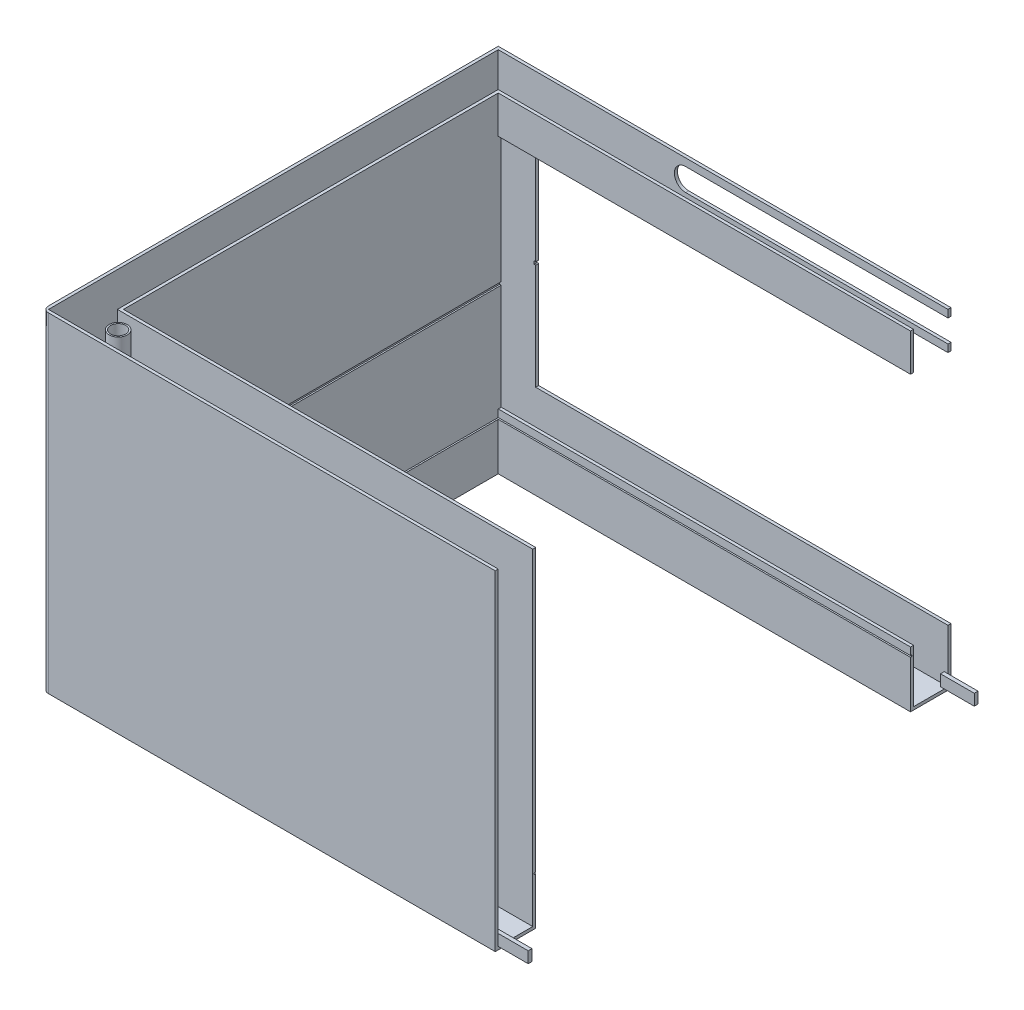
SolidWorks part; units mm, degrees
material "PVC Rigid"
ref_plane "Front Plane" through (0, 0, 0) normal (0, 0, 1) x (1, 0, 0)
ref_plane "Top Plane" through (0, 0, 0) normal (0, 1, 0) x (1, 0, 0)
ref_plane "Right Plane" through (0, 0, 0) normal (1, 0, 0) x (0, 0, -1)
sketch "Sketch1" plane through (0, 0, 0) normal (0, 1, 0) x (1, 0, 0)
  line L0 (0, -300) -> (0, 300) construction
  line L1 (0, 300) -> (-600, 300)
  line L2 (-600, 300) -> (-600, -300)
  line L3 (-600, -300) -> (0, -300)
  line L4 (0, -300) -> (0, -304)
  line L5 (0, -304) -> (-604, -304)
  line L6 (-604, -304) -> (-604, 304)
  line L7 (-604, 304) -> (0, 304)
  line L8 (0, 304) -> (0, 300)
  point P4 (0, 0)
extrude "Boss-Extrude1" add sketch "Sketch1" along normal blind 440
sketch "Sketch2" plane through (0, 0, 0) normal (0, 1, 0) x (1, 0, 0)
  line L0 (0, 0) -> (0, 250) construction
  line L1 (0, 250) -> (-550, 250)
  line L2 (-550, 250) -> (-550, -250)
  line L3 (-550, -250) -> (0, -250)
  line L4 (0, -250) -> (0, -254)
  line L5 (0, -254) -> (-554, -254)
  line L6 (-554, -254) -> (-554, 254)
  line L7 (-554, 254) -> (0, 254)
  line L8 (0, 254) -> (0, 250)
extrude "Boss-Extrude2" add sketch "Sketch2" along normal blind 440 separate body
sketch "Sketch3" plane through (0, 0, 0) normal (0, 1, 0) x (1, 0, 0)
  line L0 (0, -254) -> (0, -300)
  line L1 (0, -300) -> (-600, -300)
  line L2 (-600, -300) -> (-600, 300)
  line L3 (-600, 300) -> (0, 300)
  line L4 (0, 300) -> (0, 254)
  line L5 (0, 254) -> (-554, 254)
  line L6 (-554, 254) -> (-554, -254)
  line L7 (-554, -254) -> (0, -254)
extrude "Boss-Extrude3" add sketch "Sketch3" along normal blind 4
sketch "Sketch4" plane through (-550, 0, 0) normal (1, 0, 0) x (0, 0, -1)
  line L0 (0, 440) -> (0, 220) construction
  line L1 (-250, 440) -> (250, 440) construction
  line L2 (-250, 220) -> (250, 220)
  line L3 (250, 440) -> (250, 0) construction
  line L4 (-250, 220) -> (-250, 216)
  line L5 (-250, 440) -> (-250, 0) construction
  line L6 (-250, 216) -> (250, 216)
  line L7 (250, 216) -> (250, 220)
  line L8 (-250, 440) -> (-250, 0) construction
  point P10 (0, 220)
extrude "Cut-Extrude1" cut sketch "Sketch4" against normal blind 2
ref_plane "Plane1" through (0, 64, 0) normal (0, 1, 0) x (1, 0, 0)
sketch "Sketch7" plane through (0, 64, 0) normal (0, 1, 0) x (1, 0, 0)
  line L0 (-550, 250) -> (0, 250)
  line L1 (0, 250) -> (0, 252)
  line L2 (0, 250) -> (0, 254) construction
  line L3 (0, 252) -> (-552, 252)
  line L4 (-552, 252) -> (-552, -252)
  line L5 (-552, -252) -> (0, -252)
  line L6 (0, -254) -> (0, -250) construction
  line L7 (0, -252) -> (0, -250)
  line L8 (0, -250) -> (-550, -250)
  line L9 (-550, -250) -> (-550, 250)
extrude "Cut-Extrude3" cut sketch "Sketch7" against normal blind 1 and the other way blind 1
ref_plane "Plane2" through (0, 42, 0) normal (0, 1, 0) x (1, 0, 0)
ref_plane "Plane3" through (0, 0, 0) normal (1, 0, 0) x (0, 0, -1)
sketch "Sketch11" plane through (0, 0, 0) normal (1, 0, 0) x (0, 0, -1)
  line L0 (-295, 4) -> (-300, 4)
  line L1 (-300, 4) -> (-300, 19)
  line L9 (-300, 4) -> (-254, 4) construction
  line L10 (-300, 440) -> (-300, 4) construction
  line L11 (-295, 4) -> (-295, 19)
  line L12 (-295, 19) -> (-300, 19)
  point P0 (-295, 4)
  dimension "D1" = 5
sketch "Sketch12" plane through (0, 0, 0) normal (1, 0, 0) x (0, 0, -1)
  line L0 (254, 4) -> (300, 4) construction
  line L1 (300, 440) -> (300, 4) construction
  line L7 (300, 19) -> (295, 19)
  line L8 (295, 19) -> (295, 4)
  line L9 (295, 4) -> (300, 4)
  line L10 (300, 4) -> (300, 19)
  point P0 (295, 4)
  dimension "D1" = 5
extrude "Boss-Extrude4" add sketch "Sketch12" along normal blind 40 and the other way blind 5 separate body contours L7 L8 L9 L10
extrude "Boss-Extrude5" add sketch "Sketch11" along normal blind 40 and the other way blind 5 separate body contours L12 L1 L0 L11
sketch "Sketch13" plane through (0, 0, -304) normal (0, 0, -1) x (-1, 0, 0)
  line L0 (0, 440) -> (0, 0) construction
  line L1 (0, 440) -> (604, 440) construction
  line L2 (0, 390) -> (550, 390)
  line L3 (550, 390) -> (550, 220)
  line L4 (550, 220) -> (552, 220)
  line L5 (552, 220) -> (552, 216)
  line L8 (550, 75) -> (0, 75)
  line L9 (0, 75) -> (0, 390)
  line L10 (552, 216) -> (550, 216)
  line L11 (550, 216) -> (550, 75)
  point P0 (0, 390)
  dimension "D1" = 50
extrude "Cut-Extrude5" cut sketch "Sketch13" against normal up to vertex contours L2 L3 L4 L5 L10 L11 L8 L9
sketch "Sketch14" plane through (0, 0, -304) normal (0, 0, -1) x (-1, 0, 0)
  line L0 (0, 400) -> (0, 430)
  line L1 (0, 440) -> (0, 390) construction
  line L3 (0, 430) -> (350, 430)
  line L5 (0, 400) -> (350, 400)
  arc A0 (350, 430) -> (350, 400) centre (350, 415) cw
  point P6 (0, 415)
extrude "Cut-Extrude6" cut sketch "Sketch14" against normal blind 4
fillet "Fillet1" radius 8 1 edges at (-604, 220, 304)
sketch "Sketch15" plane through (0, 0, 0) normal (0, -1, 0) x (1, 0, 0)
  line L0 (-604, -304) -> (-604, 296) construction
  line L1 (0, -304) -> (-604, -304) construction
  line L2 (-600, -300) -> (-588, -300)
  line L3 (-588, -300) -> (-588, -298)
  line L4 (-588, -298) -> (-598, -298)
  line L5 (-598, -298) -> (-598, -288)
  line L6 (-598, -288) -> (-600, -288)
  line L7 (-600, -288) -> (-600, -300)
  point P0 (-600, -300)
  dimension "D1" = 4
  dimension "D2" = 4
extrude "Cut-Extrude7" cut sketch "Sketch15" against normal blind 2
mirror "Mirror1" about plane through (0, 0, 0) normal (0, 0, 1) of "Cut-Extrude7"
sketch "Sketch16" plane through (-552, 0, 0) normal (1, 0, 0) x (0, 0, -1)
  line L0 (254, 220) -> (-250, 220) construction
  line L1 (-254, 218) -> (254, 218) construction
  line L2 (254, 216) -> (254, 220) construction
  line L3 (-254, 208) -> (254, 208) construction
  point P0 (0, 218)
  point P8 (0, 218)
  point P11 (0, 208)
  dimension "D1" = 2
  dimension "D2" = 10
sketch "Sketch17" plane through (0, 4, 0) normal (0, 1, 0) x (1, 0, 0)
  line L0 (-600, 300) -> (-600, -300) construction
  line L1 (-600, -300) -> (0, -300) construction
  circle A0 centre (-530, -277) radius 10
  dimension "D1" = 70
  dimension "D2" = 23
extrude "Cut-Extrude8" cut sketch "Sketch17" against normal blind 10
sketch "Sketch18" plane through (0, 4, 0) normal (0, 1, 0) x (1, 0, 0)
  circle A0 centre (-530, -277) radius 10
  circle A1 centre (-530, -277) radius 12
extrude "Boss-Extrude6" add sketch "Sketch18" along normal up to surface (436 mm away) contours A0 | A1 up to face at (-276, 440, 0)
sketch "Sketch19" plane through (0, 0, 250) normal (0, 0, -1) x (-1, 0, 0)
  line L0 (0, 440) -> (0, 65) construction
  line L1 (0, 65) -> (550, 65) construction
  circle A0 centre (530, 85) radius 10
  dimension "D1" = 530
  dimension "D2" = 20
extrude "Cut-Extrude9" cut sketch "Sketch19" against normal blind 25
sketch "Sketch20" plane through (0, 0, 254) normal (0, 0, 1) x (1, 0, 0)
  circle A0 centre (-530, 85) radius 10
  circle A1 centre (-530, 85) radius 12
extrude "Boss-Extrude7" add sketch "Sketch20" along normal blind 23
